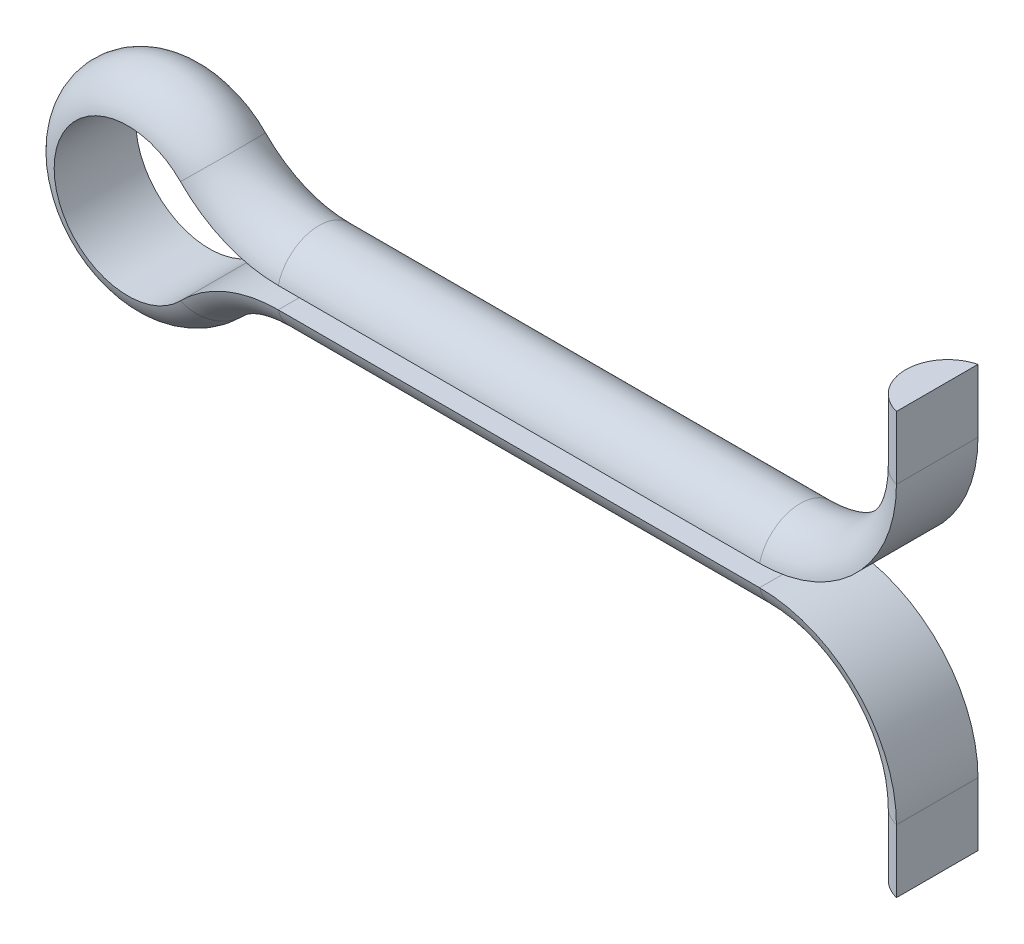
SolidWorks part; units mm, degrees
ref_plane "Přední rovina" through (0, 0, 0) normal (0, 0, 1) x (1, 0, 0)
ref_plane "Horní rovina" through (0, 0, 0) normal (0, 1, 0) x (1, 0, 0)
ref_plane "Pravá rovina" through (0, 0, 0) normal (1, 0, 0) x (0, 0, -1)
sketch "Skica2" plane through (0, 0, 0) normal (0, 0, 1) x (1, 0, 0)
  line L0 (35, 10) -> (35, 7)
  line L1 (30, 2) -> (7.1414, 2)
  line L2 (7.1414, -2) -> (30, -2)
  line L3 (35, -7) -> (35, -10)
  arc A0 (35, 7) -> (30, 2) centre (30, 7) cw
  arc A1 (7.1414, 2) -> (3.5707, 3.5) centre (7.1414, 7) cw
  arc A2 (30, -2) -> (35, -7) centre (30, -7) cw
  arc A3 (3.5707, 3.5) -> (3.5707, -3.5) centre (0, 0) ccw
  arc A4 (7.1414, -2) -> (3.5707, -3.5) centre (7.1414, -7) ccw
  point P16 (18.5707, -2)
  dimension "D3" = 5
  dimension "D4" = 5
  dimension "D5" = 5
  dimension "D1" = 35
  dimension "D2" = 4
  dimension "D6" = 10
ref_plane "Rovina1" through (35, 10, 0) normal (0, -1, 0) x (-1, 0, 0)
sketch "Skica4" plane through (35, 10, 0) normal (0, -1, 0) x (-1, 0, 0)
  line L1 (-2, 0) -> (0, 0) construction
  line L2 (-1.5, 1.9365) -> (-1.5, -1.9365)
  arc A0 (-1.5, -1.9365) -> (-1.5, 1.9365) centre (-2, 0) ccw
  point P0 (-1.5, -1.9365)
  dimension "D1" = 2
  dimension "D2" = 1.5
sweep "Táhnout po křivce1" add profiles "Skica4" path "Skica2"
